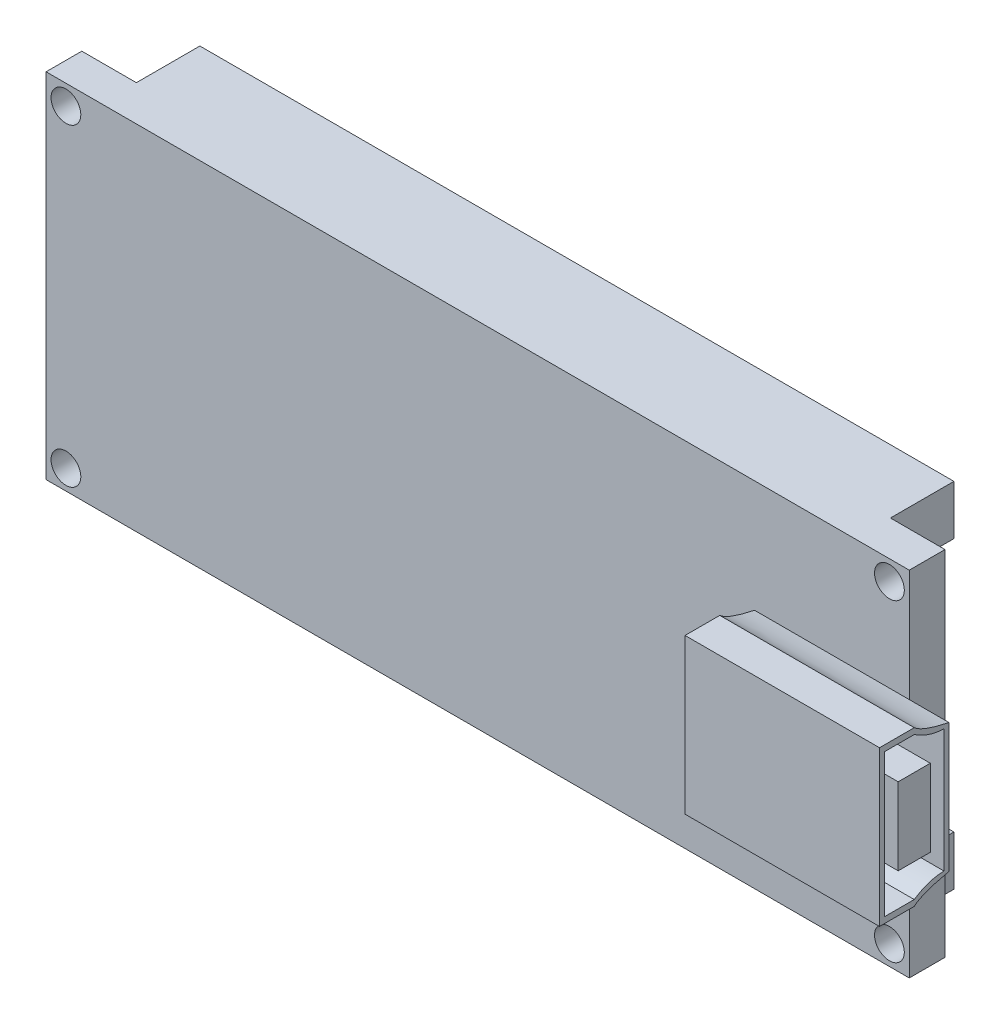
SolidWorks part; units mm, degrees
ref_plane "Front Plane" through (0, 0, 0) normal (0, 0, 1) x (1, 0, 0)
ref_plane "Top Plane" through (0, 0, 0) normal (0, 1, 0) x (1, 0, 0)
ref_plane "Right Plane" through (0, 0, 0) normal (1, 0, 0) x (0, 0, -1)
sketch "Sketch1" plane through (0, 0, 0) normal (0, 0, 1) x (1, 0, 0)
  line L0 (0, 8.9) -> (0, -8.9) construction
  line L1 (21.75, -8.9) -> (-21.75, -8.9)
  line L2 (21.75, -8.9) -> (21.75, 8.9)
  line L3 (21.75, 8.9) -> (-21.75, 8.9)
  line L4 (-21.75, -8.9) -> (-21.75, 8.9)
  line L5 (21.75, -8.9) -> (-21.75, 8.9) construction
  line L6 (21.75, 8.9) -> (-21.75, -8.9) construction
  line L7 (-21.75, 8.9) -> (-20.75, 8.9)
  line L8 (-21.75, 8.9) -> (-21.75, 7.9)
  line L9 (-21.75, 7.9) -> (-20.75, 7.9) construction
  line L10 (-20.75, 8.9) -> (-20.75, 7.9) construction
  line L11 (-21.75, 0) -> (21.75, 0) construction
  circle A0 centre (-20.75, 7.9) radius 0.75
  circle A1 centre (20.75, 7.9) radius 0.75
  circle A2 centre (20.75, -7.9) radius 0.75
  circle A3 centre (-20.75, -7.9) radius 0.75
  point P0 (0, 0)
  dimension "D3" = 1
  dimension "D5" = 1.5
  dimension "D1" = 17.8
  dimension "D2" = 43.5
  dimension "D4" = 1
extrude "Boss-Extrude1" add sketch "Sketch1" along normal blind 1.8 contours L4 L1 L2 L3 A1 A0 A2 A3
sketch "Sketch2" plane through (0, 0, 1.8) normal (0, 0, 1) x (1, 0, 0)
  line L0 (21.75, 0) -> (13.95, 0) construction
  line L1 (21.75, -8.9) -> (21.75, 8.9) construction
  line L2 (13.95, 3.9) -> (13.95, -3.9)
  line L3 (13.95, 3.9) -> (23.75, 3.9)
  line L4 (23.75, 3.9) -> (23.75, -3.9)
  line L5 (23.75, -3.9) -> (13.95, -3.9)
  point P7 (13.95, 0)
  dimension "D1" = 7.8
  dimension "D2" = 7.8
  dimension "D3" = 9.8
extrude "Boss-Extrude2" add sketch "Sketch2" along normal blind 3.5
sketch "Sketch3" plane through (23.75, 0, 0) normal (1, 0, 0) x (0, 0, -1)
  line L0 (-1.8, -3.25) -> (-1.8, 3.25) construction
  line L1 (-1.8, -3.9) -> (-1.8, 3.9) construction
  line L2 (-3.55, 3.9) -> (-1.8, 3.9)
  line L3 (-5.3, 3.9) -> (-1.8, 3.9) construction
  line L4 (-1.8, 3.9) -> (-1.8, 3.25)
  line L5 (-3.55, -3.9) -> (-1.8, -3.9)
  line L6 (-5.3, -3.9) -> (-1.8, -3.9) construction
  line L7 (-1.8, -3.9) -> (-1.8, -3.25)
  line L8 (-1.8, 0) -> (-5.3, 0) construction
  line L9 (-5.3, -3.9) -> (-5.3, 3.9) construction
  spline S0 degree 2 poles (-1.8, -3.25) (-3.1385, -3.5282) (-3.55, -3.9) knots 0 0 0 0.396074 0.396074 0.396074
  spline S1 degree 2 poles (-1.8, 3.25) (-3.1385, 3.5282) (-3.55, 3.9) knots 0 0 0 0.396074 0.396074 0.396074
  point P5 (-1.8, 0)
  dimension "D1" = 6.5
extrude "Cut-Extrude1" cut sketch "Sketch3" against normal through all
sketch "Sketch4" plane through (23.75, 0, 0) normal (1, 0, 0) x (0, 0, -1)
  line L0 (-5.3, 0) -> (-1.8, 0) construction
  line L1 (-5.3, -3.9) -> (-5.3, 3.9) construction
  line L2 (-1.8, -3.25) -> (-1.8, 3.25) construction
  line L3 (-3.55, -3.9) -> (-3.55, -3.6) construction
  line L4 (-3.55, -3.6) -> (-5.05, -3.6)
  line L5 (-2.05, -3.1058) -> (-2.05, 3.1058)
  line L6 (-3.55, 3.6) -> (-5.05, 3.6)
  line L7 (-5.05, -3.6) -> (-5.05, 3.6)
  line L8 (-2.2512, -3.117) -> (-5.05, 3.6) construction
  line L9 (-2.2512, 3.117) -> (-5.05, -3.6) construction
  line L10 (-2.7404, -1.9431) -> (-4.3596, -1.9431)
  line L11 (-2.7404, -1.9431) -> (-2.7404, 1.9431)
  line L12 (-2.7404, 1.9431) -> (-4.3596, 1.9431)
  line L13 (-4.3596, -1.9431) -> (-4.3596, 1.9431)
  line L14 (-2.7404, -1.9431) -> (-4.3596, 1.9431) construction
  line L15 (-2.7404, 1.9431) -> (-4.3596, -1.9431) construction
  spline S0 degree 2 poles (-3.55, -3.6) (-2.8375, -3.1193) (-2.05, -3.1058) knots 0 0 0 0.945733 0.945733 0.945733
  spline S1 degree 2 poles (-3.55, 3.6) (-2.8375, 3.1193) (-2.05, 3.1058) knots 0 0 0 0.945733 0.945733 0.945733
  point P6 (-3.55, 0)
  point P11 (-3.55, 0)
  dimension "D3" = 3.8862
  dimension "D4" = 1.6192
extrude "Cut-Extrude2" cut sketch "Sketch4" against normal blind 8.5 contours L5 S1 L6 L7 L4 S0 | L11 L10 L13 L12
sketch "Sketch5" plane through (0, 0, 0) normal (0, 0, -1) x (-1, 0, 0)
  line L0 (0, 8.9) -> (0, 6.4) construction
  line L1 (-21.75, 8.9) -> (21.75, 8.9) construction
  line L2 (-21.75, 0) -> (21.75, 0) construction
  line L3 (19, 6.4) -> (-19, 6.4)
  line L4 (19, 6.4) -> (19, 8.9)
  line L5 (19, 8.9) -> (-19, 8.9)
  line L6 (-19, 6.4) -> (-19, 8.9)
  line L7 (19, 6.4) -> (-19, 8.9) construction
  line L8 (19, 8.9) -> (-19, 6.4) construction
  line L9 (-21.75, -8.9) -> (-21.75, 8.9) construction
  line L10 (21.75, -8.9) -> (21.75, 8.9) construction
  line L11 (19, -6.4) -> (19, -8.9)
  line L12 (-19, -6.4) -> (-19, -8.9)
  line L13 (19, -6.4) -> (-19, -6.4)
  line L14 (19, -8.9) -> (-19, -8.9)
  point P5 (0, 7.65)
  dimension "D1" = 2.5
  dimension "D2" = 2.5
  dimension "D3" = 38
extrude "Boss-Extrude3" add sketch "Sketch5" along normal blind 3.2
